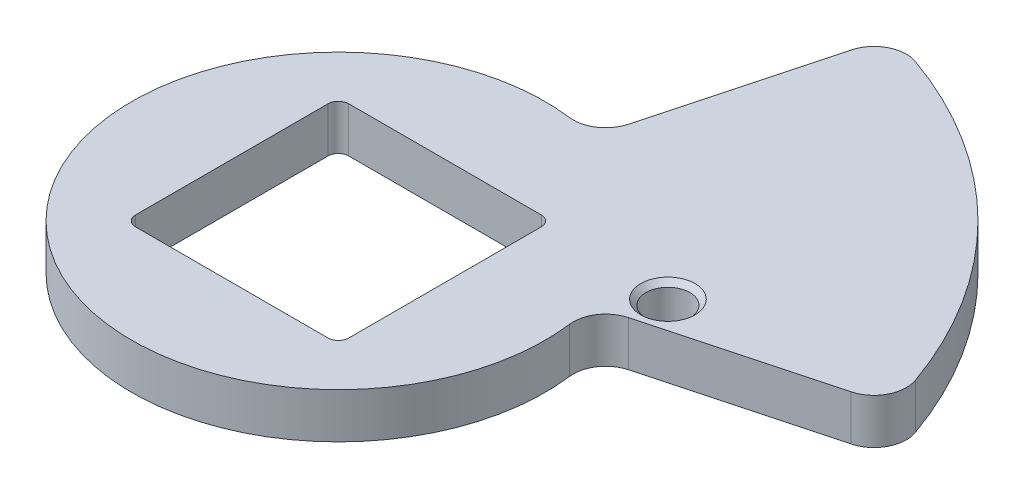
SolidWorks part; units mm, degrees
ref_plane "Front Plane" through (0, 0, 0) normal (0, 0, 1) x (1, 0, 0)
ref_plane "Top Plane" through (0, 0, 0) normal (0, 1, 0) x (1, 0, 0)
ref_plane "Right Plane" through (0, 0, 0) normal (1, 0, 0) x (0, 0, -1)
sketch "Sketch3" plane through (0, 0, 0) normal (0, 1, 0) x (1, 0, 0)
  line L0 (0, -43.7575) -> (0, 55.6085) construction
  line L1 (-55.1527, 0) -> (56.672, 0) construction
  line L2 (0, 0) -> (54.7728, 54.7728) construction
  line L3 (10.6511, 39.7505) -> (6.0252, 22.4863)
  line L4 (22.86, 27.8747) -> (22.86, -39.642) construction
  line L5 (-9.4615, -10.4775) -> (9.4615, -10.4775)
  line L6 (-10.4775, -9.4615) -> (-10.4775, 9.4615)
  line L7 (-9.4615, 10.4775) -> (9.4615, 10.4775)
  line L8 (10.4775, -9.4615) -> (10.4775, 9.4615)
  line L9 (-10.4775, -10.4775) -> (10.4775, 10.4775) construction
  line L10 (-10.4775, 10.4775) -> (10.4775, -10.4775) construction
  line L11 (39.7505, 10.6511) -> (22.4863, 6.0252)
  line L12 (0, 0) -> (19.6276, 5.2592) construction
  arc A0 (2.5586, 20.1583) -> (20.1583, 2.5586) centre (0, 0) ccw
  arc A2 (14.7731, 41.9232) -> (41.9232, 14.7731) centre (0, 0) cw
  circle A3 centre (22.86, 9.525) radius 2.159
  arc A4 (-9.4615, -10.4775) -> (-10.4775, -9.4615) centre (-9.4615, -9.4615) cw
  arc A5 (9.4615, -10.4775) -> (10.4775, -9.4615) centre (9.4615, -9.4615) ccw
  arc A6 (9.4615, 10.4775) -> (10.4775, 9.4615) centre (9.4615, 9.4615) cw
  arc A7 (-10.4775, 9.4615) -> (-9.4615, 10.4775) centre (-9.4615, 9.4615) cw
  arc A8 (22.4863, 6.0252) -> (20.1583, 2.5586) centre (23.308, 2.9584) ccw
  arc A9 (6.0252, 22.4863) -> (2.5586, 20.1583) centre (2.9584, 23.308) cw
  arc A10 (41.9232, 14.7731) -> (39.7505, 10.6511) centre (38.9287, 13.7179) cw
  arc A11 (14.7731, 41.9232) -> (10.6511, 39.7505) centre (13.7179, 38.9287) ccw
  dimension "D1" = 45
  dimension "D6" = 44.45
  dimension "D7" = 4.318
  dimension "D10" = 1.016
  dimension "D11" = 3.175
  dimension "D12" = 3.175
  dimension "D2" = 15
  dimension "D3" = 20.955
  dimension "D4" = 20.955
  dimension "D5" = 22.86
  dimension "D8" = 22.86
  dimension "D9" = 9.525
extrude "Boss-Extrude1" add sketch "Sketch3" along normal blind 4.445
chamfer "Chamfer1" distance 0.508 angle 45 2 edges at (22.86, 0, -7.366) (22.86, 4.445, -7.366)
